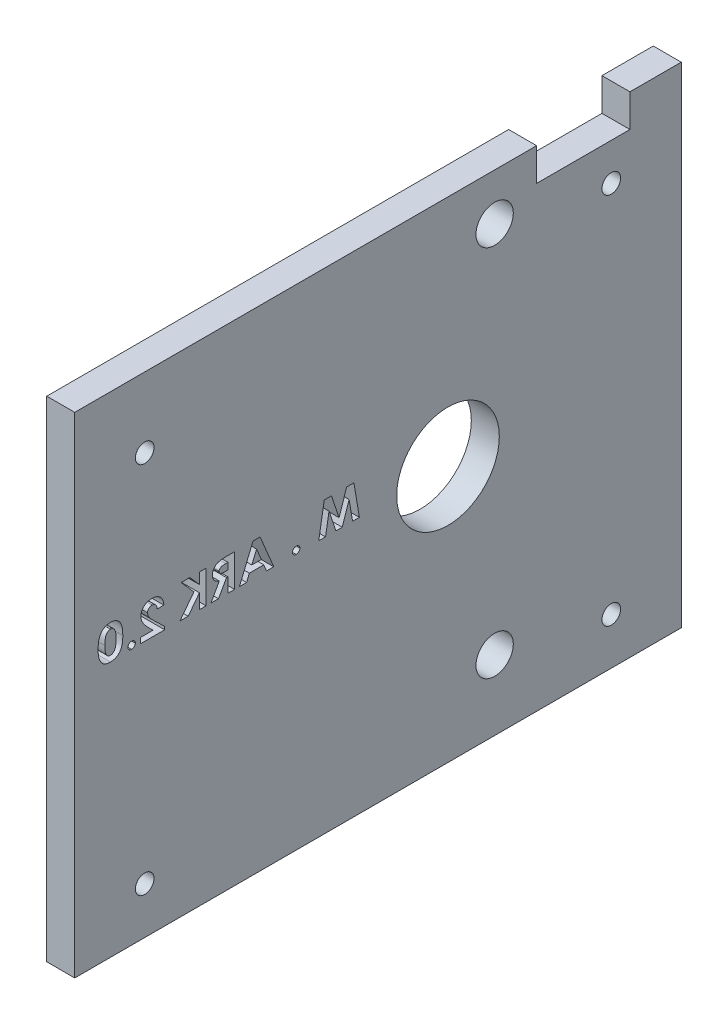
SolidWorks part; units mm, degrees
material "Acrylic (Medium-high impact)"
ref_plane "Front Plane" through (0, 0, 0) normal (0, 0, 1) x (1, 0, 0)
ref_plane "Top Plane" through (0, 0, 0) normal (0, 1, 0) x (1, 0, 0)
ref_plane "Right Plane" through (0, 0, 0) normal (1, 0, 0) x (0, 0, -1)
sketch "Sketch1" plane through (0, 0, 0) normal (1, 0, 0) x (0, 0, -1)
  line L0 (-1000, 0) -> (49000, 0) construction
  line L1 (-80, -250) -> (320, -250)
  line L6 (-900, -190) -> (49100, -190) construction
  line L7 (0, -1000) -> (0, 49000) construction
  line L10 (-80, -190) -> (-80, -250)
  line L11 (-30, 50) -> (-30, -120.0496)
  line L12 (84.8849, -120.0496) -> (-119.1387, -120.0496) construction
  line L20 (0, -750) -> (0, 49250) construction
  line L30 (320, -190) -> (320, -250)
  line L31 (50, 50) -> (50, -120)
  line L32 (-30, 50) -> (50, 50)
  line L33 (120, -190) -> (320, -190)
  line L34 (-27.1942, 0) -> (27.1942, 0) construction
  line L38 (50, -55) -> (-30, -55)
  line L39 (10, -950) -> (10, 49050) construction
  line L40 (39, 50) -> (19, 50)
  line L41 (39, 50) -> (39, 43)
  line L42 (39, 43) -> (19, 43)
  line L43 (19, 50) -> (19, 43)
  circle A1 centre (0, 0) radius 11
  circle A2 centre (10, -40) radius 4
  circle A3 centre (10, 40) radius 4
  arc A5 (120, -190) -> (50, -120) centre (120, -120) cw
  arc A8 (-80, -190) -> (-30, -120.0496) centre (-103.9305, -120.0496) ccw
  point P0 (0, 0)
  point P51 (0, 0)
  dimension "D7" = 73.9305
  dimension "D14" = 22
  dimension "D16" = 40
  dimension "D18" = 120
  dimension "D12" = 70
  dimension "D13" = 7
  dimension "D20" = 9
  dimension "D6" = 10
  dimension "D22" = 8
  dimension "D2" = 400
  dimension "D3" = 50
  dimension "D4" = 30
  dimension "D5" = 250
  dimension "D8" = 300
  dimension "D9" = 70
  dimension "D11" = 60
  dimension "D10" = 50
  dimension "D15" = 50
  dimension "D17" = 40
  dimension "D19" = 20
  dimension "D21" = 105
extrude "Boss-Extrude1" add sketch "Sketch1" along normal blind 6
sketch "Sketch4" plane through (0, 0, 0) normal (-1, 0, 0) x (0, 0, 1)
  line L0 (-50, -55) -> (30, -55) construction
  line L1 (80, -55) -> (30, -55)
  line L2 (80, -55) -> (80, 50)
  line L3 (80, 50) -> (30, 50)
  line L4 (30, -55) -> (30, 50)
extrude "Boss-Extrude2" add sketch "Sketch4" against normal blind 6
sketch "Sketch5" plane through (0, 0, 0) normal (-1, 0, 0) x (0, 0, 1)
  line L0 (65, -965.5732) -> (65, 49034.4268) construction
  line L1 (80, -55) -> (80, 50) construction
  line L2 (80, 50) -> (-19, 50) construction
  line L3 (-50, -55) -> (80, -55) construction
  line L4 (-935, 35) -> (49065, 35) construction
  line L5 (-935, -45) -> (49065, -45) construction
  line L6 (-50, 50) -> (-50, -55) construction
  line L7 (-35, -965) -> (-35, 49035) construction
  circle A0 centre (65, 35) radius 2
  circle A1 centre (65, -45) radius 2
  circle A2 centre (-35, 35) radius 2
  circle A3 centre (-35, -45) radius 2
  point P22 (0, 0)
  dimension "D2" = 15
  dimension "D3" = 10
  dimension "D4" = 4
  dimension "D5" = 15
  dimension "D1" = 15
extrude "Cut-Extrude1" cut sketch "Sketch5" against normal up to next
sketch "Sketch6" plane through (0, 0, 0) normal (-1, 0, 0) x (0, 0, 1)
  line L0 (17.6082, 0) -> (76.4653, 0) construction
  line L1 (-50, -55) -> (80, -55) construction
  text T0 "M . ARK 2.0" font "Century Gothic" height 7
  dimension "D1" = 55
extrude "Cut-Extrude2" cut sketch "Sketch6" against normal up to next
